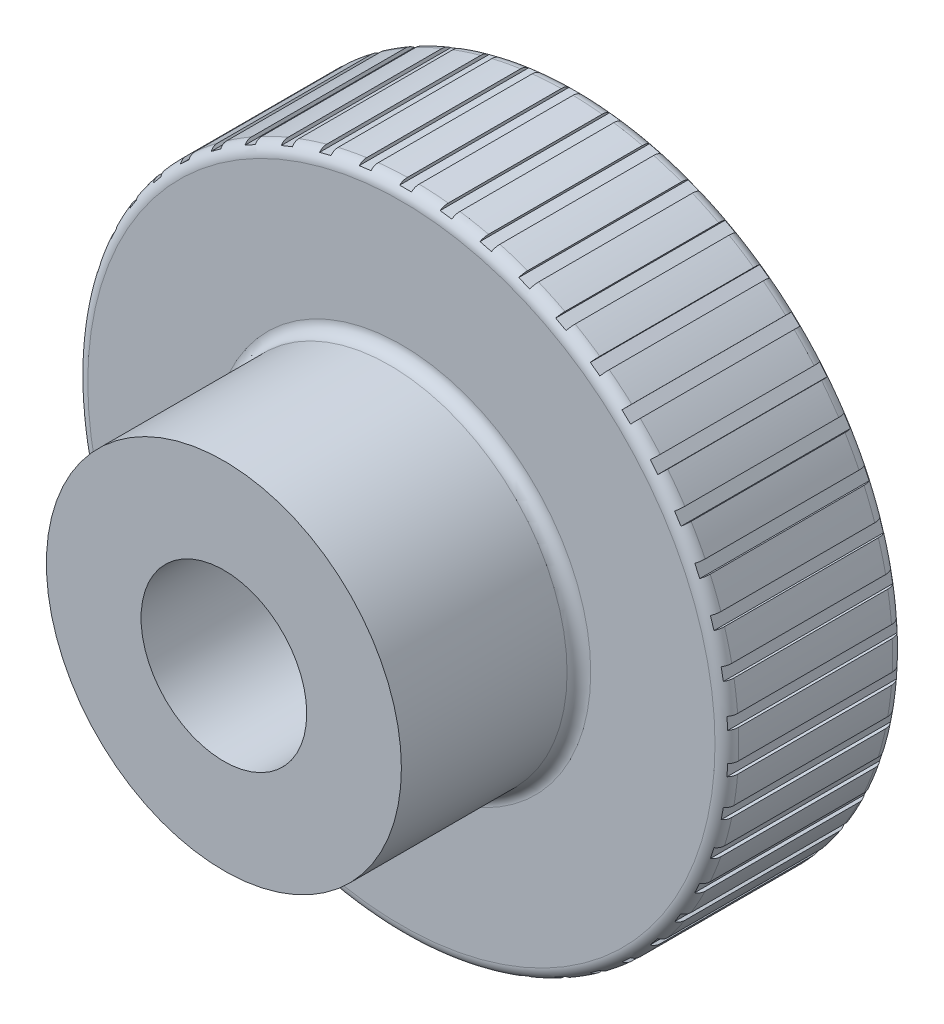
SolidWorks part; units mm, degrees
ref_plane "Спереди" through (0, 0, 0) normal (0, 0, 1) x (1, 0, 0)
ref_plane "Сверху" through (0, 0, 0) normal (0, 1, 0) x (1, 0, 0)
ref_plane "Справа" through (0, 0, 0) normal (1, 0, 0) x (0, 0, -1)
sketch "Sketch1" plane through (0, 0, 0) normal (0, 0, 1) x (1, 0, 0)
  circle A0 centre (0, 0) radius 5.5
  dimension "D1" = 11
extrude "Boss-Extrude1" add sketch "Sketch1" along normal blind 3
sketch "Sketch2" plane through (0, 0, 3) normal (0, 0, 1) x (1, 0, 0)
  circle A0 centre (0, 0) radius 3
  dimension "D1" = 6
extrude "Boss-Extrude2" add sketch "Sketch2" along normal blind 3
hole_wizard "M8 Tapped Hole1" positions "Sketch4" profile "Sketch3" tap size "M8" standard "ISO" end condition through all
sketch "Sketch4" plane through (0, 0, 6) normal (0, 0, 1) x (1, 0, 0)
  point P0 (0, 0)
sketch "Sketch3" plane through (0, 0, 6) normal (1, 0, 0) x (0, -1, 0)
  line L0 (0, 0) -> (0, 6)
  line L1 (0, 6) -> (1.4, 6)
  line L2 (1.4, 6) -> (1.4, 0)
  line L5 (1.4, 0) -> (0, 0)
  line L11 (0, -6.35) -> (0, 107.95) construction
  dimension "Thru Tap Drill Dia." = 2.8
  dimension "Thru Tap Drill Depth" = 6
cosmetic thread "Hole Thread1" parameters "D2"=3
fillet "Fillet1" radius 0.2 3 edges at (3, 0, 3) (5.5, 0, 3) (5.5, 0, 0)
sketch "Sketch5" plane through (0, 0, 0) normal (0, 0, -1) x (-1, 0, 0)
  line L1 (-0.1014, 5.45) -> (0.0986, 5.45)
  line L2 (-0.1014, 5.45) -> (0, 11.9614)
  line L3 (0, 11.9614) -> (0.0986, 5.45)
  dimension "D1" = 0.2
  dimension "D2" = 5.45
extrude "Enlèv. mat.-Extru.2" cut sketch "Sketch5" against normal blind 10 contours L2 L3 L1
pattern_circular "Répétition circulaire1" count 50 over 360 about axis through (0, 0, 0) along (0, 0, 1) of "Enlèv. mat.-Extru.2"
